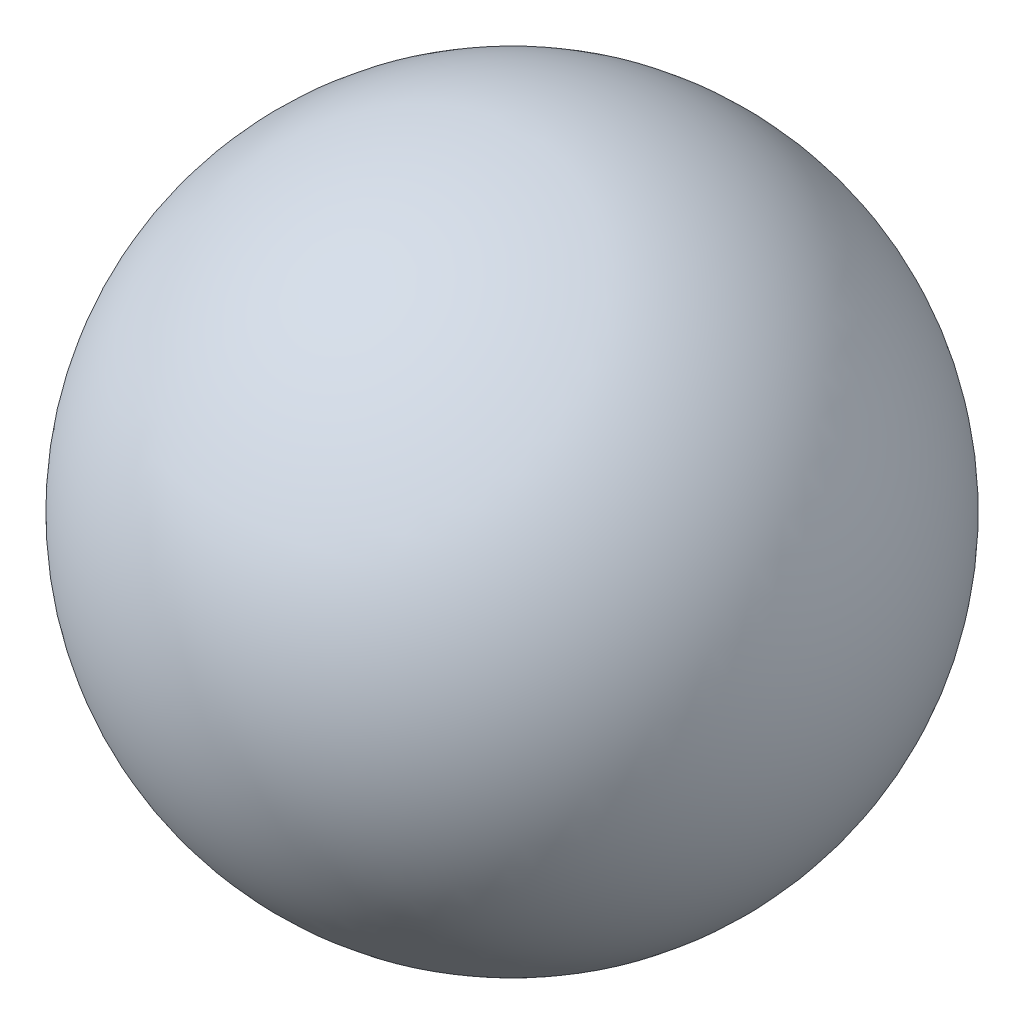
SolidWorks part; units mm, degrees
ref_plane "Front Plane" through (0, 0, 0) normal (0, 0, 1) x (1, 0, 0)
ref_plane "Top Plane" through (0, 0, 0) normal (0, 1, 0) x (1, 0, 0)
ref_plane "Right Plane" through (0, 0, 0) normal (1, 0, 0) x (0, 0, -1)
sketch "Sketch1" plane through (0, 0, 0) normal (0, 0, 1) x (1, 0, 0)
  line L0 (0, 3.4327) -> (0, -3.4327)
  arc A0 (0, -3.4327) -> (0, 3.4327) centre (0, 0) ccw
  dimension "D1" = 6.8653
revolve "Revolve1" add sketch "Sketch1" angle 360 about L0
